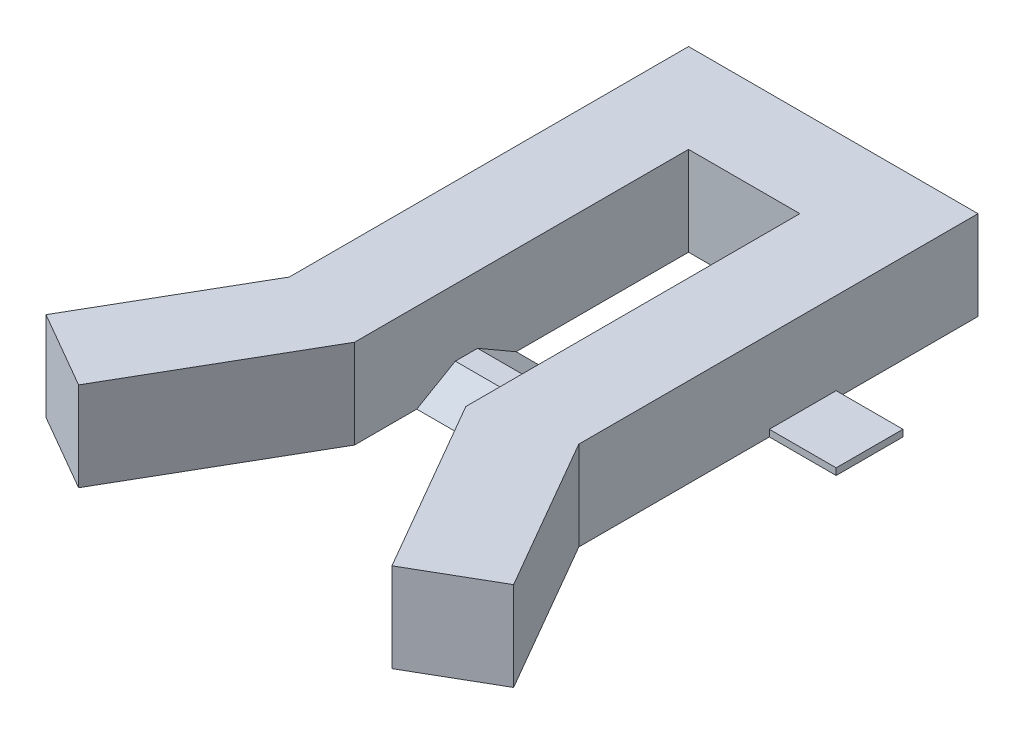
SolidWorks part; units mm, degrees
ref_plane "Front Plane" through (0, 0, 0) normal (0, 0, 1) x (1, 0, 0)
ref_plane "Top Plane" through (0, 0, 0) normal (0, 1, 0) x (1, 0, 0)
ref_plane "Right Plane" through (0, 0, 0) normal (1, 0, 0) x (0, 0, -1)
sketch "Sketch2" plane through (0, 0, 0) normal (0, 1, 0) x (1, 0, 0)
  line L0 (-35.1795, -39.282) -> (-12.5, 0)
  line L3 (-32.5, 95) -> (-32.5, 5.359)
  line L4 (-32.5, 5.359) -> (-52.5, -29.282)
  line L5 (-52.5, -29.282) -> (-35.1795, -39.282)
  line L6 (-32.5, 95) -> (0, 95)
  line L7 (0, 95) -> (0, 75)
  line L8 (0, 75) -> (-12.5, 75)
  line L9 (-12.5, 75) -> (-12.5, 0)
  point P2 (-35.514, -41.8637)
  dimension "D1" = 20
  dimension "D3" = 12.5
  dimension "D2" = 20
  dimension "D4" = 20
  dimension "D5" = 75
  dimension "D6" = 30
  dimension "D7" = 40
extrude "Boss-Extrude1" add sketch "Sketch2" along normal blind 20
mirror "Mirror3" about plane through (0, 0, 0) normal (1, 0, 0) of "Boss-Extrude1"
sketch "Sketch4" plane through (12.5, 0, 0) normal (-1, 0, 0) x (0, 0, 1)
  line L0 (0, 0) -> (-75, 0) construction
  line L1 (-75, 0) -> (0, 0) construction
  line L2 (-75, 0) -> (-75, 20) construction
  line L3 (-36.2917, 0) -> (-27.6314, 5)
  line L4 (-27.6314, 5) -> (-22.6314, 5)
  line L5 (-22.6314, 5) -> (-13.9711, 0)
  line L6 (-13.9711, 0) -> (-36.2917, 0)
  circle A0 centre (-45, 32.5) radius 32.5 construction
  point P14 (-4.7174, 0)
  point P15 (-6.6091, 0)
  point P16 (-32.4647, 0)
  dimension "D1" = 65
  dimension "D2" = 30
  dimension "D3" = 30
  dimension "D4" = 5
  dimension "D5" = 5
extrude "Boss-Extrude2" add sketch "Sketch4" along normal up to surface (25 mm away) up to face at (-12.5, 10, -37.5)
sketch "Sketch6" plane through (0, 0, 0) normal (0, -1, 0) x (1, 0, 0)
  line L0 (-12.5, -36.2917) -> (-12.5, -75) construction
  line L1 (-12.5, -75) -> (0, -75) construction
  line L2 (-12.5, -75) -> (12.5, -75) construction
  line L3 (0, -75) -> (0, 0) construction
  line L4 (-32.5, -95) -> (-32.5, -5.359) construction
  line L5 (-32.5, -48.1458) -> (-47.5, -48.1458)
  line L6 (-32.5, -48.1458) -> (-32.5, -63.1458)
  line L7 (-32.5, -63.1458) -> (-47.5, -63.1458)
  line L8 (-47.5, -48.1458) -> (-47.5, -63.1458)
  line L9 (32.5, -63.1458) -> (47.5, -63.1458)
  line L10 (47.5, -48.1458) -> (47.5, -63.1458)
  line L11 (32.5, -48.1458) -> (47.5, -48.1458)
  line L12 (32.5, -48.1458) -> (32.5, -63.1458)
  point P15 (-32.5, -55.6458)
  point P16 (-12.5, -55.6458)
  dimension "D1" = 15
  dimension "D2" = 15
extrude "Boss-Extrude3" add sketch "Sketch6" against normal blind 1.5
equation "\"D3@Sketch2\"=25/2"
equation "\"D2@Sketch2\"=\"D1@Sketch2\""
equation "\"D4@Sketch2\"=\"D2@Sketch2\""
equation "\"D3@Sketch4\"=\"D2@Sketch4\""
